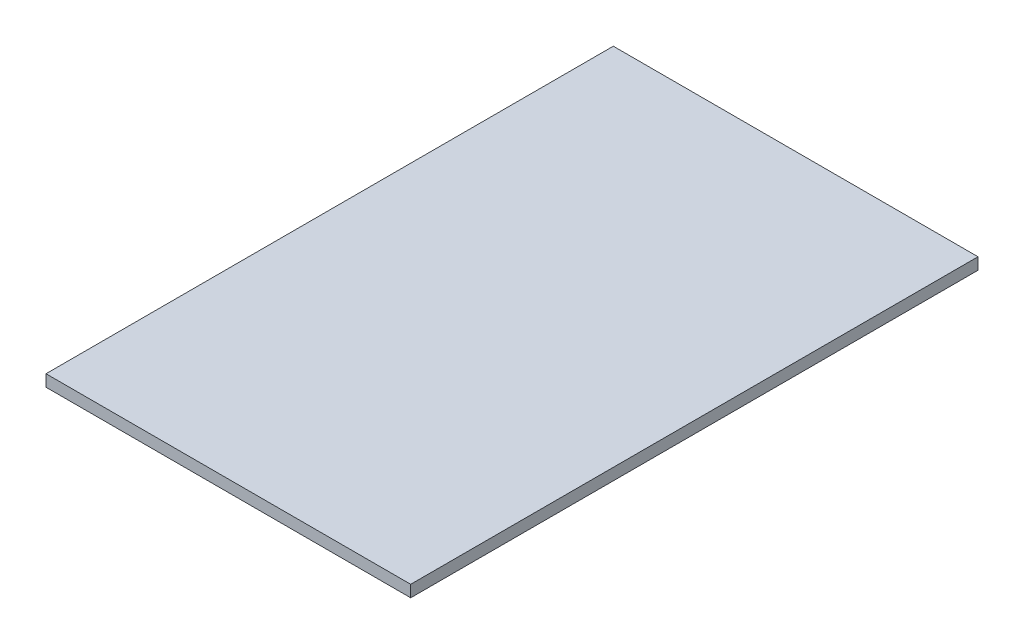
SolidWorks part; units mm, degrees
material "Copper"
ref_plane "Front Plane" through (0, 0, 0) normal (0, 0, 1) x (1, 0, 0)
ref_plane "Top Plane" through (0, 0, 0) normal (0, 1, 0) x (1, 0, 0)
ref_plane "Right Plane" through (0, 0, 0) normal (1, 0, 0) x (0, 0, -1)
sketch "Sketch3" plane through (0, 0, 0) normal (0, 1, 0) x (1, 0, 0)
  line L1 (0, 0) -> (49.5, 0)
  line L2 (0, 0) -> (0, 77)
  line L3 (0, 77) -> (49.5, 77)
  line L4 (49.5, 0) -> (49.5, 77)
  dimension "D1" = 77
  dimension "D2" = 49.5
extrude "Boss-Extrude1" add sketch "Sketch3" along normal blind 1.59
